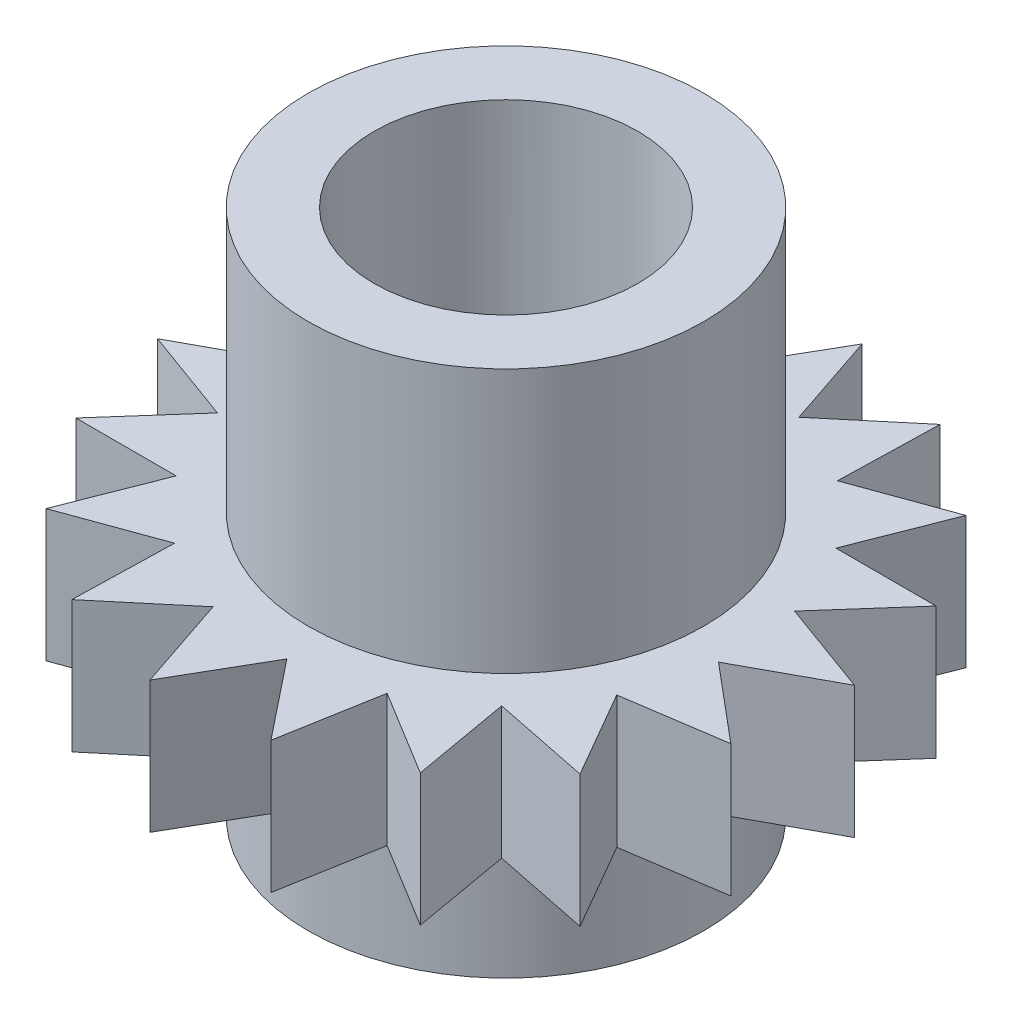
SolidWorks part; units mm, degrees
ref_plane "Front Plane" through (0, 0, 0) normal (0, 0, 1) x (1, 0, 0)
ref_plane "Top Plane" through (0, 0, 0) normal (0, 1, 0) x (1, 0, 0)
ref_plane "Right Plane" through (0, 0, 0) normal (1, 0, 0) x (0, 0, -1)
sketch "Sketch1" plane through (0, 0, 0) normal (0, 1, 0) x (1, 0, 0)
  line L0 (-0.669, 8.9751) -> (1.2322, 12.2653)
  line L1 (1.2322, 12.2653) -> (2.441, 8.6627)
  line L2 (5.3529, 11.1041) -> (5.2566, 7.3054)
  line L3 (2.441, 8.6627) -> (5.3529, 11.1041)
  line L4 (8.8279, 8.6037) -> (7.4382, 5.0669)
  line L5 (5.2566, 7.3054) -> (8.8279, 8.6037)
  line L6 (11.2382, 5.0655) -> (8.7226, 2.2174)
  line L7 (7.4382, 5.0669) -> (11.2382, 5.0655)
  line L8 (12.2929, 0.9163) -> (8.9549, -0.8996)
  line L9 (8.7226, 2.2174) -> (12.2929, 0.9163)
  line L10 (11.865, -3.3433) -> (8.1072, -3.9082)
  line L11 (8.9549, -0.8996) -> (11.865, -3.3433)
  line L12 (10.0059, -7.1998) -> (6.2816, -6.4453)
  line L13 (8.1072, -3.9082) -> (10.0059, -7.1998)
  line L14 (6.94, -10.1878) -> (3.6983, -8.205)
  line L15 (6.2816, -6.4453) -> (6.94, -10.1878)
  line L16 (3.0371, -11.947) -> (0.669, -8.9751)
  line L17 (3.6983, -8.205) -> (3.0371, -11.947)
  line L18 (-1.2322, -12.2653) -> (-2.441, -8.6627)
  line L19 (0.669, -8.9751) -> (-1.2322, -12.2653)
  line L20 (-5.3529, -11.1041) -> (-5.2566, -7.3054)
  line L21 (-2.441, -8.6627) -> (-5.3529, -11.1041)
  line L22 (-8.8279, -8.6037) -> (-7.4382, -5.0669)
  line L23 (-5.2566, -7.3054) -> (-8.8279, -8.6037)
  line L24 (-11.2382, -5.0655) -> (-8.7226, -2.2174)
  line L25 (-7.4382, -5.0669) -> (-11.2382, -5.0655)
  line L26 (-12.2929, -0.9163) -> (-8.9549, 0.8996)
  line L27 (-8.7226, -2.2174) -> (-12.2929, -0.9163)
  line L28 (-11.865, 3.3433) -> (-8.1072, 3.9082)
  line L29 (-8.9549, 0.8996) -> (-11.865, 3.3433)
  line L30 (-10.0059, 7.1998) -> (-6.2816, 6.4453)
  line L31 (-8.1072, 3.9082) -> (-10.0059, 7.1998)
  line L32 (-6.94, 10.1878) -> (-3.6983, 8.205)
  line L33 (-6.2816, 6.4453) -> (-6.94, 10.1878)
  line L34 (-3.0371, 11.947) -> (-0.669, 8.9751)
  line L35 (-3.6983, 8.205) -> (-3.0371, 11.947)
  circle A0 centre (0, 0) radius 9
  point P60 (0, 0)
  dimension "D1" = 18
  dimension "D2" = 3.8
extrude "Boss-Extrude1" add sketch "Sketch1" along normal blind 5 contours A0 | L20 L23 L22 L25 L24 L27 L26 L29 L28 L31 L30 L33 L32 L35 L34 L0 L1 L3 L2 L5 L4 L7 L6 L9 L8 L11 L10 L13 L12 L15 L14 L17 L16 L19 L18 L21
sketch "Sketch2" plane through (0, 5, 0) normal (0, 1, 0) x (1, 0, 0)
  circle A0 centre (0, 0) radius 7.5
  dimension "D1" = 15
extrude "Boss-Extrude2" add sketch "Sketch2" along normal mid plane 20
sketch "Sketch3" plane through (0, 15, 0) normal (0, 1, 0) x (1, 0, 0)
  circle A0 centre (0, 0) radius 5
  dimension "D1" = 10
extrude "Cut-Extrude1" cut sketch "Sketch3" against normal blind 20
sketch "Sketch4" plane through (0, 5, 0) normal (0, 1, 0) x (1, 0, 0)
  line L1 (-2, 6) -> (2, 6)
  line L2 (-2, 6) -> (-2, 4)
  line L3 (-2, 4) -> (2, 4)
  line L4 (2, 6) -> (2, 4)
  line L5 (-2, 6) -> (2, 4) construction
  line L6 (-2, 4) -> (2, 6) construction
  circle A0 centre (0, 0) radius 5 construction
  point P0 (0, 5)
  dimension "D1" = 4
  dimension "D2" = 2
extrude "Boss-Extrude3" add sketch "Sketch4" against normal blind 10
